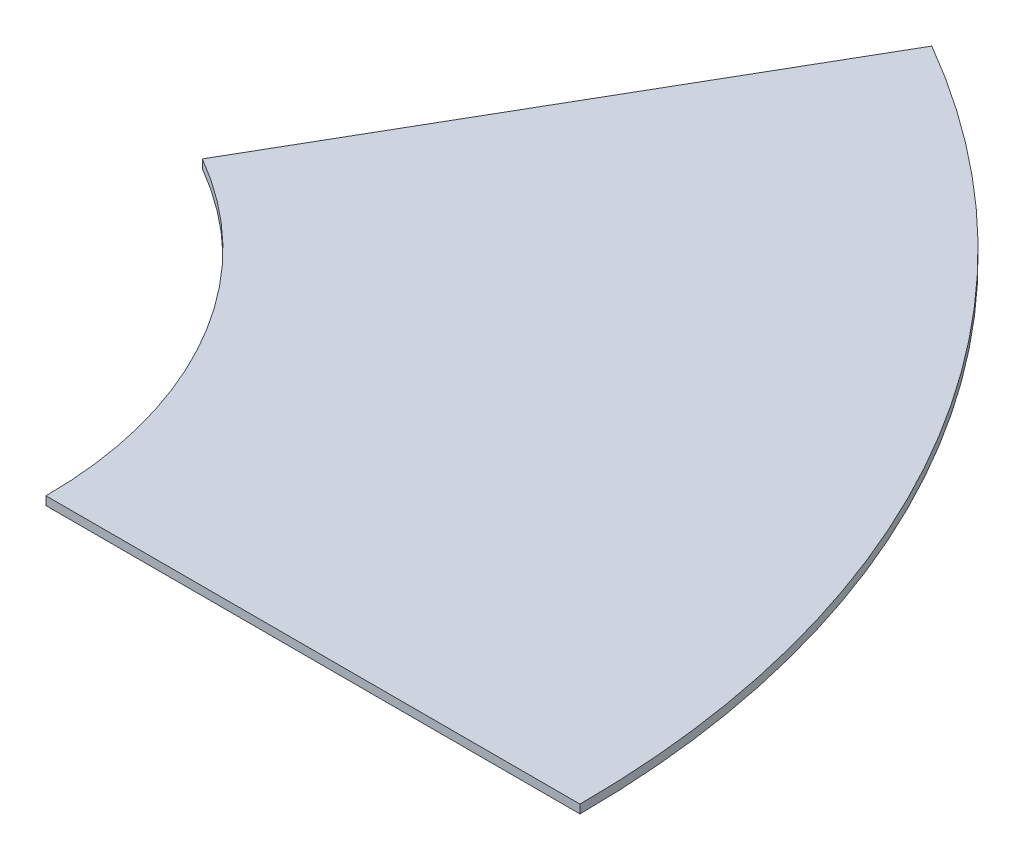
SolidWorks part; units mm, degrees
ref_plane "Plan de face" through (0, 0, 0) normal (0, 0, 1) x (1, 0, 0)
ref_plane "Plan de dessus" through (0, 0, 0) normal (0, 1, 0) x (1, 0, 0)
ref_plane "Plan de droite" through (0, 0, 0) normal (1, 0, 0) x (0, 0, -1)
sketch "Esquisse1" plane through (0, 0, 0) normal (0, 1, 0) x (1, 0, 0)
  line L0 (0, 0) -> (10, 0) construction
  line L1 (0, 0) -> (5, 8.6603) construction
  line L2 (10, 0) -> (22.5, 0)
  line L3 (11.25, 19.4856) -> (5, 8.6603)
  arc A0 (10, 0) -> (5, 8.6603) centre (0, 0) ccw
  arc A1 (22.5, 0) -> (11.25, 19.4856) centre (0, 0) ccw
  point P5 (10.1816, 0)
  point P8 (0, 0)
  dimension "D2" = 22.5
  dimension "D1" = 10
  dimension "D3" = 60
sketch "Esquisse2" plane through (0, 0, 0) normal (0, 1, 0) x (1, 0, 0)
  line L0 (8.6603, 5) -> (19.4856, 11.25) construction
  arc A0 (10, 0) -> (5, 8.6603) centre (0, 0) ccw construction
  arc A1 (22.5, 0) -> (11.25, 19.4856) centre (0, 0) ccw construction
  circle A2 centre (16.25, 9.3819) radius 11.2731 construction
extrude "Boss.-Extru.2" add sketch "Esquisse1" against normal blind 0.2
